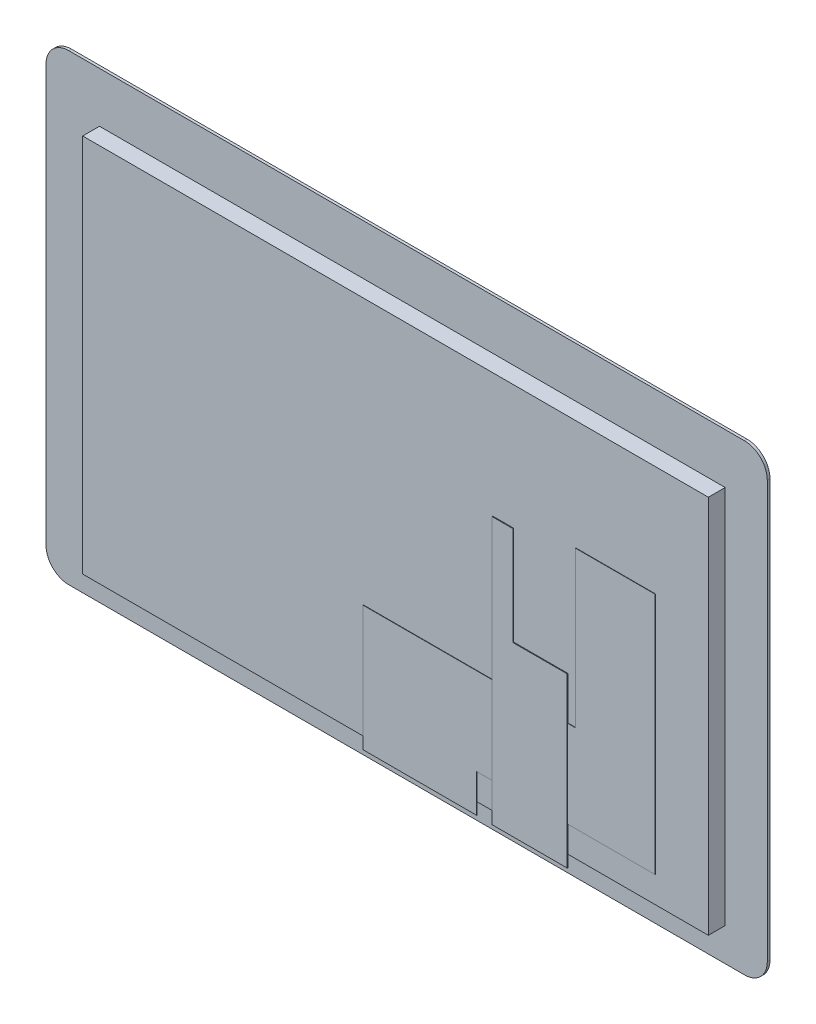
SolidWorks part; units mm, degrees
ref_plane "Front Plane" through (0, 0, 0) normal (0, 0, 1) x (1, 0, 0)
ref_plane "Top Plane" through (0, 0, 0) normal (0, 1, 0) x (1, 0, 0)
ref_plane "Right Plane" through (0, 0, 0) normal (1, 0, 0) x (0, 0, -1)
sketch "Sketch1" plane through (0, 0, 0) normal (0, 0, 1) x (1, 0, 0)
  line L0 (0, -55) -> (0, 55) construction
  line L1 (-89.04, 60.96) -> (89.04, 60.96)
  line L2 (-95.04, 54.96) -> (-95.04, -54.96)
  line L3 (-89.04, -60.96) -> (89.04, -60.96)
  line L4 (95.04, 54.96) -> (95.04, -54.96)
  line L5 (55, 0) -> (-55, 0) construction
  arc A0 (89.04, -60.96) -> (95.04, -54.96) centre (89.04, -54.96) ccw
  arc A1 (-95.04, -54.96) -> (-89.04, -60.96) centre (-89.04, -54.96) ccw
  arc A2 (-89.04, 60.96) -> (-95.04, 54.96) centre (-89.04, 54.96) ccw
  arc A3 (89.04, 60.96) -> (95.04, 54.96) centre (89.04, 54.96) cw
  dimension "D5" = 6
  dimension "D1" = 95.04
  dimension "D2" = 95.04
  dimension "D3" = 60.96
  dimension "D4" = 60.96
extrude "Boss-Extrude1" add sketch "Sketch1" along normal blind 0.7
sketch "Sketch2" plane through (0, 0, 0) normal (0, 0, 1) x (1, 0, 0)
  line L0 (89.04, 60.96) -> (-89.04, 60.96) construction
  line L1 (-76.92, 42.81) -> (76.92, 42.81)
  line L2 (-76.92, 42.81) -> (-76.92, -42.82)
  line L3 (-76.92, -42.82) -> (76.92, -42.82)
  line L4 (76.92, 42.81) -> (76.92, -42.82)
  line L5 (95.04, -54.96) -> (95.04, 54.96) construction
  dimension "D1" = 18.15
  dimension "D2" = 18.12
  dimension "D3" = 153.84
  dimension "D4" = 85.63
extrude "Cut-Extrude1" cut sketch "Sketch2" along normal blind 0.8
sketch "Sketch3" plane through (0, 0, 0) normal (0, 0, 1) x (1, 0, 0)
  line L0 (-76.92, -42.82) -> (76.92, -42.82) construction
  line L1 (-76.92, 42.81) -> (76.92, 42.81)
  line L2 (-76.92, 42.81) -> (-76.92, -42.82)
  line L3 (-76.92, -42.82) -> (76.92, -42.82)
  line L4 (76.92, 42.81) -> (76.92, -42.82)
  line L5 (76.92, -42.82) -> (76.92, 42.81) construction
extrude "Boss-Extrude4" add sketch "Sketch3" along normal blind 0.75 and the other way blind 0.05
sketch "Sketch4" plane through (0, 0, 0.7) normal (0, 0, 1) x (1, 0, 0)
  line L1 (-80.96, 47.74) -> (83.94, 47.74)
  line L2 (-80.96, 47.74) -> (-80.96, -52.26)
  line L3 (-80.96, -52.26) -> (83.94, -52.26)
  line L4 (83.94, 47.74) -> (83.94, -52.26)
  line L7 (95.04, -54.96) -> (95.04, 54.96) construction
  line L8 (89.04, 60.96) -> (-89.04, 60.96) construction
  dimension "D1" = 164.9
  dimension "D2" = 11.1
  dimension "D3" = 100
  dimension "D4" = 13.22
extrude "Boss-Extrude5" add sketch "Sketch4" along normal blind 4.43
sketch "Sketch5" plane through (0, 0, 5.13) normal (0, 0, 1) x (1, 0, 0)
  line L0 (-80.96, -52.26) -> (83.94, -52.26) construction
  line L1 (48.9957, 18.69) -> (69.9957, 18.69)
  line L2 (48.9957, 18.69) -> (48.9957, -22.31)
  line L4 (69.9957, 18.69) -> (69.9957, -45.31)
  line L5 (-7.0043, -22.31) -> (48.9957, -22.31)
  line L7 (22.9957, -45.31) -> (69.9957, -45.31)
  line L10 (-7.0043, -22.31) -> (-7.0043, -55.31)
  line L11 (-7.0043, -55.31) -> (22.9957, -55.31)
  line L12 (22.9957, -45.31) -> (22.9957, -55.31)
  dimension "D1" = 70.95
  dimension "D2" = 64
  dimension "D3" = 21
  dimension "D4" = 41
  dimension "D5" = 56
  dimension "D6" = 30
  dimension "D7" = 33
extrude "Boss-Extrude6" add sketch "Sketch5" along normal blind 0.1
sketch "Sketch6" plane through (0, 0, 5.13) normal (0, 0, 1) x (1, 0, 0)
  line L1 (32.59, 15.01) -> (27.09, 15.01)
  line L2 (32.59, 15.01) -> (32.59, -10.99)
  line L4 (27.09, 15.01) -> (27.09, -55.31)
  line L5 (46.94, -10.99) -> (32.59, -10.99)
  line L6 (46.94, -10.99) -> (46.94, -55.31)
  line L9 (-80.96, -52.26) -> (-7.0043, -52.26) construction
  line L10 (83.94, -52.26) -> (83.94, 47.74) construction
  line L13 (27.09, -55.31) -> (46.94, -55.31)
  dimension "D1" = 67.27
  dimension "D2" = 5.5
  dimension "D3" = 26
  dimension "D4" = 19.85
  dimension "D5" = 37
extrude "Boss-Extrude7" add sketch "Sketch6" along normal blind 0.2
sketch "Sketch7" plane through (0, 0, 0) normal (0, 0, 1) x (1, 0, 0)
  line L0 (-12.6042, 0) -> (11.4575, 0) construction
  line L1 (2.959, 0) -> (-2.959, 0) construction
  line L2 (0, 11.0885) -> (0, -10.2932) construction
  line L3 (0, -2.959) -> (0, 2.959) construction
sketch "Sketch8" plane through (0, 0, 5.13) normal (0, 0, 1) x (1, 0, 0)
  line L0 (-89.04, 60.96) -> (89.04, 60.96)
  line L1 (-95.04, 54.96) -> (-95.04, -54.96)
  line L2 (-89.04, -60.96) -> (89.04, -60.96)
  line L3 (95.04, 54.96) -> (95.04, -54.96)
  line L5 (-89.04, 70.96) -> (89.04, 70.96)
  line L6 (105.04, 54.96) -> (105.04, -54.96)
  line L7 (-89.04, -70.96) -> (89.04, -70.96)
  line L8 (-105.04, 54.96) -> (-105.04, -54.96)
  arc A0 (89.04, -60.96) -> (95.04, -54.96) centre (89.04, -54.96) ccw
  arc A1 (-95.04, -54.96) -> (-89.04, -60.96) centre (-89.04, -54.96) ccw
  arc A2 (-89.04, 60.96) -> (-95.04, 54.96) centre (-89.04, 54.96) ccw
  arc A3 (89.04, 60.96) -> (95.04, 54.96) centre (89.04, 54.96) cw
  arc A4 (89.04, 70.96) -> (105.04, 54.96) centre (89.04, 54.96) cw
  arc A5 (89.04, -70.96) -> (105.04, -54.96) centre (89.04, -54.96) ccw
  arc A6 (-105.04, -54.96) -> (-89.04, -70.96) centre (-89.04, -54.96) ccw
  arc A7 (-89.04, 70.96) -> (-105.04, 54.96) centre (-89.04, 54.96) ccw
  dimension "D1" = 6
  dimension "D2" = 10
